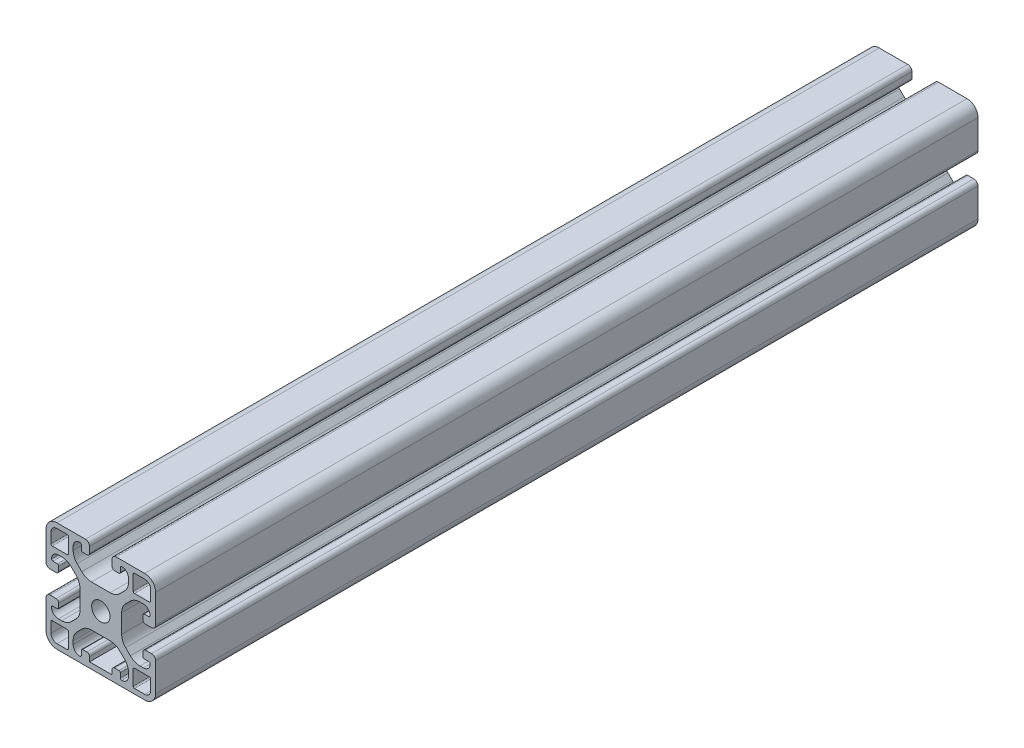
SolidWorks part; units mm, degrees
ref_plane "Ebene vorne" through (0, 0, 0) normal (0, 0, 1) x (1, 0, 0)
ref_plane "Ebene oben" through (0, 0, 0) normal (0, 1, 0) x (1, 0, 0)
ref_plane "Ebene rechts" through (0, 0, 0) normal (1, 0, 0) x (0, 0, -1)
ref_plane "Ebene1" through (0, 0, 1000) normal (0, 0, 1) x (1, 0, 0)
sketch "Skizze1" plane through (0, 0, 1000) normal (0, 0, 1) x (1, 0, 0)
  line L0 (27.8, 32.3) -> (27.8, 37.7)
  line L1 (28.3, 38.2) -> (32, 38.2)
  line L2 (34.2, 36) -> (34.2, 32.3)
  line L3 (33.7, 31.8) -> (28.3, 31.8)
  line L4 (28.3, 8.2) -> (33.7, 8.2)
  line L5 (34.2, 7.7) -> (34.2, 4)
  line L6 (32, 1.8) -> (28.3, 1.8)
  line L7 (27.8, 2.3) -> (27.8, 7.7)
  line L8 (3.7, 31.8) -> (-1.7, 31.8)
  line L9 (-2.2, 32.3) -> (-2.2, 36)
  line L10 (0, 38.2) -> (3.7, 38.2)
  line L11 (4.2, 37.7) -> (4.2, 32.3)
  line L12 (4.2, 7.7) -> (4.2, 2.3)
  line L13 (3.7, 1.8) -> (0, 1.8)
  line L14 (-2.2, 4) -> (-2.2, 7.7)
  line L15 (-1.7, 8.2) -> (3.7, 8.2)
  line L16 (20.1, 2) -> (11.9, 2)
  line L17 (11.9, 2) -> (11.9, 3.65)
  line L18 (10.9, 4.65) -> (9.4, 4.65)
  line L19 (8.9, 4.15) -> (8.9, 2.5)
  line L20 (5.9, 4.5) -> (5.9, 5.7076)
  line L21 (7.3645, 9.2431) -> (9.0569, 10.9355)
  line L22 (12.5924, 12.4) -> (19.4076, 12.4)
  line L23 (22.9431, 10.9355) -> (24.6355, 9.2431)
  line L24 (26.1, 5.7076) -> (26.1, 4.5)
  line L25 (23.1, 2.5) -> (23.1, 4.15)
  line L26 (22.6, 4.65) -> (21.1, 4.65)
  line L27 (20.1, 3.65) -> (20.1, 2)
  line L28 (5.9, 34.2924) -> (5.9, 35.5)
  line L29 (8.9, 37.5) -> (8.9, 35.85)
  line L30 (9.4, 35.35) -> (10.9, 35.35)
  line L31 (11.9, 36.35) -> (11.9, 38.5)
  line L32 (10.4, 40) -> (0, 40)
  line L33 (-4, 36) -> (-4, 25.6)
  line L34 (-2.5, 24.1) -> (-0.35, 24.1)
  line L35 (0.65, 25.1) -> (0.65, 26.6)
  line L36 (0.15, 27.1) -> (-1.5, 27.1)
  line L37 (0.5, 30.1) -> (1.7076, 30.1)
  line L38 (5.2431, 28.6355) -> (6.9355, 26.9431)
  line L39 (8.4, 23.4076) -> (8.4, 16.5924)
  line L40 (6.9355, 13.0569) -> (5.2431, 11.3645)
  line L41 (1.7076, 9.9) -> (0.5, 9.9)
  line L42 (-1.5, 12.9) -> (0.15, 12.9)
  line L43 (0.65, 13.4) -> (0.65, 14.9)
  line L44 (-0.35, 15.9) -> (-2.5, 15.9)
  line L45 (-4, 14.4) -> (-4, 4)
  line L46 (0, 0) -> (32, 0)
  line L47 (36, 4) -> (36, 14.4)
  line L48 (34.5, 15.9) -> (32.35, 15.9)
  line L49 (31.35, 14.9) -> (31.35, 13.4)
  line L50 (31.85, 12.9) -> (33.5, 12.9)
  line L51 (31.5, 9.9) -> (30.2924, 9.9)
  line L52 (26.7569, 11.3645) -> (25.0645, 13.0569)
  line L53 (23.6, 16.5924) -> (23.6, 23.4076)
  line L54 (25.0645, 26.9431) -> (26.7569, 28.6355)
  line L55 (30.2924, 30.1) -> (31.5, 30.1)
  line L56 (33.5, 27.1) -> (31.85, 27.1)
  line L57 (31.35, 26.6) -> (31.35, 25.1)
  line L58 (32.35, 24.1) -> (34.5, 24.1)
  line L59 (36, 25.6) -> (36, 36)
  line L60 (32, 40) -> (21.6, 40)
  line L61 (20.1, 38.5) -> (20.1, 36.35)
  line L62 (21.1, 35.35) -> (22.6, 35.35)
  line L63 (23.1, 35.85) -> (23.1, 37.5)
  line L64 (26.1, 35.5) -> (26.1, 34.2924)
  line L65 (24.6355, 30.7569) -> (22.9431, 29.0645)
  line L66 (19.4076, 27.6) -> (12.5924, 27.6)
  line L67 (9.0569, 29.0645) -> (7.3645, 30.7569)
  circle A0 centre (16, 20) radius 3.35
  arc A1 (28.3, 31.8) -> (27.8, 32.3) centre (28.3, 32.3) cw
  arc A2 (27.8, 37.7) -> (28.3, 38.2) centre (28.3, 37.7) cw
  arc A3 (32, 38.2) -> (34.2, 36) centre (32, 36) cw
  arc A4 (34.2, 32.3) -> (33.7, 31.8) centre (33.7, 32.3) cw
  arc A5 (27.8, 7.7) -> (28.3, 8.2) centre (28.3, 7.7) cw
  arc A6 (33.7, 8.2) -> (34.2, 7.7) centre (33.7, 7.7) cw
  arc A7 (34.2, 4) -> (32, 1.8) centre (32, 4) cw
  arc A8 (28.3, 1.8) -> (27.8, 2.3) centre (28.3, 2.3) cw
  arc A9 (4.2, 32.3) -> (3.7, 31.8) centre (3.7, 32.3) cw
  arc A10 (-1.7, 31.8) -> (-2.2, 32.3) centre (-1.7, 32.3) cw
  arc A11 (-2.2, 36) -> (0, 38.2) centre (0, 36) cw
  arc A12 (3.7, 38.2) -> (4.2, 37.7) centre (3.7, 37.7) cw
  arc A13 (3.7, 8.2) -> (4.2, 7.7) centre (3.7, 7.7) cw
  arc A14 (4.2, 2.3) -> (3.7, 1.8) centre (3.7, 2.3) cw
  arc A15 (0, 1.8) -> (-2.2, 4) centre (0, 4) cw
  arc A16 (-2.2, 7.7) -> (-1.7, 8.2) centre (-1.7, 7.7) cw
  arc A17 (11.9, 3.65) -> (10.9, 4.65) centre (10.9, 3.65) ccw
  arc A18 (9.4, 4.65) -> (8.9, 4.15) centre (9.4, 4.15) ccw
  arc A19 (8.9, 2.5) -> (8.4, 2) centre (8.4, 2.5) cw
  arc A20 (8.4, 2) -> (5.9, 4.5) centre (8.4, 4.5) cw
  arc A21 (5.9, 5.7076) -> (7.3645, 9.2431) centre (10.9, 5.7076) cw
  arc A22 (9.0569, 10.9355) -> (12.5924, 12.4) centre (12.5924, 7.4) cw
  arc A23 (19.4076, 12.4) -> (22.9431, 10.9355) centre (19.4076, 7.4) cw
  arc A24 (24.6355, 9.2431) -> (26.1, 5.7076) centre (21.1, 5.7076) cw
  arc A25 (26.1, 4.5) -> (23.6, 2) centre (23.6, 4.5) cw
  arc A26 (23.6, 2) -> (23.1, 2.5) centre (23.6, 2.5) cw
  arc A27 (23.1, 4.15) -> (22.6, 4.65) centre (22.6, 4.15) ccw
  arc A28 (21.1, 4.65) -> (20.1, 3.65) centre (21.1, 3.65) ccw
  arc A29 (7.3645, 30.7569) -> (5.9, 34.2924) centre (10.9, 34.2924) cw
  arc A30 (5.9, 35.5) -> (8.4, 38) centre (8.4, 35.5) cw
  arc A31 (8.4, 38) -> (8.9, 37.5) centre (8.4, 37.5) cw
  arc A32 (8.9, 35.85) -> (9.4, 35.35) centre (9.4, 35.85) ccw
  arc A33 (10.9, 35.35) -> (11.9, 36.35) centre (10.9, 36.35) ccw
  arc A34 (11.9, 38.5) -> (10.4, 40) centre (10.4, 38.5) ccw
  arc A35 (0, 40) -> (-4, 36) centre (0, 36) ccw
  arc A36 (-4, 25.6) -> (-2.5, 24.1) centre (-2.5, 25.6) ccw
  arc A37 (-0.35, 24.1) -> (0.65, 25.1) centre (-0.35, 25.1) ccw
  arc A38 (0.65, 26.6) -> (0.15, 27.1) centre (0.15, 26.6) ccw
  arc A39 (-1.5, 27.1) -> (-2, 27.6) centre (-1.5, 27.6) cw
  arc A40 (-2, 27.6) -> (0.5, 30.1) centre (0.5, 27.6) cw
  arc A41 (1.7076, 30.1) -> (5.2431, 28.6355) centre (1.7076, 25.1) cw
  arc A42 (6.9355, 26.9431) -> (8.4, 23.4076) centre (3.4, 23.4076) cw
  arc A43 (8.4, 16.5924) -> (6.9355, 13.0569) centre (3.4, 16.5924) cw
  arc A44 (5.2431, 11.3645) -> (1.7076, 9.9) centre (1.7076, 14.9) cw
  arc A45 (0.5, 9.9) -> (-2, 12.4) centre (0.5, 12.4) cw
  arc A46 (-2, 12.4) -> (-1.5, 12.9) centre (-1.5, 12.4) cw
  arc A47 (0.15, 12.9) -> (0.65, 13.4) centre (0.15, 13.4) ccw
  arc A48 (0.65, 14.9) -> (-0.35, 15.9) centre (-0.35, 14.9) ccw
  arc A49 (-2.5, 15.9) -> (-4, 14.4) centre (-2.5, 14.4) ccw
  arc A50 (-4, 4) -> (0, 0) centre (0, 4) ccw
  arc A51 (32, 0) -> (36, 4) centre (32, 4) ccw
  arc A52 (36, 14.4) -> (34.5, 15.9) centre (34.5, 14.4) ccw
  arc A53 (32.35, 15.9) -> (31.35, 14.9) centre (32.35, 14.9) ccw
  arc A54 (31.35, 13.4) -> (31.85, 12.9) centre (31.85, 13.4) ccw
  arc A55 (33.5, 12.9) -> (34, 12.4) centre (33.5, 12.4) cw
  arc A56 (34, 12.4) -> (31.5, 9.9) centre (31.5, 12.4) cw
  arc A57 (30.2924, 9.9) -> (26.7569, 11.3645) centre (30.2924, 14.9) cw
  arc A58 (25.0645, 13.0569) -> (23.6, 16.5924) centre (28.6, 16.5924) cw
  arc A59 (23.6, 23.4076) -> (25.0645, 26.9431) centre (28.6, 23.4076) cw
  arc A60 (26.7569, 28.6355) -> (30.2924, 30.1) centre (30.2924, 25.1) cw
  arc A61 (31.5, 30.1) -> (34, 27.6) centre (31.5, 27.6) cw
  arc A62 (34, 27.6) -> (33.5, 27.1) centre (33.5, 27.6) cw
  arc A63 (31.85, 27.1) -> (31.35, 26.6) centre (31.85, 26.6) ccw
  arc A64 (31.35, 25.1) -> (32.35, 24.1) centre (32.35, 25.1) ccw
  arc A65 (34.5, 24.1) -> (36, 25.6) centre (34.5, 25.6) ccw
  arc A66 (36, 36) -> (32, 40) centre (32, 36) ccw
  arc A67 (21.6, 40) -> (20.1, 38.5) centre (21.6, 38.5) ccw
  arc A68 (20.1, 36.35) -> (21.1, 35.35) centre (21.1, 36.35) ccw
  arc A69 (22.6, 35.35) -> (23.1, 35.85) centre (22.6, 35.85) ccw
  arc A70 (23.1, 37.5) -> (23.6, 38) centre (23.6, 37.5) cw
  arc A71 (23.6, 38) -> (26.1, 35.5) centre (23.6, 35.5) cw
  arc A72 (26.1, 34.2924) -> (24.6355, 30.7569) centre (21.1, 34.2924) cw
  arc A73 (22.9431, 29.0645) -> (19.4076, 27.6) centre (19.4076, 32.6) cw
  arc A74 (12.5924, 27.6) -> (9.0569, 29.0645) centre (12.5924, 32.6) cw
extrude "Aufsatz-Linear austragen1" add sketch "Skizze1" against normal blind 300
